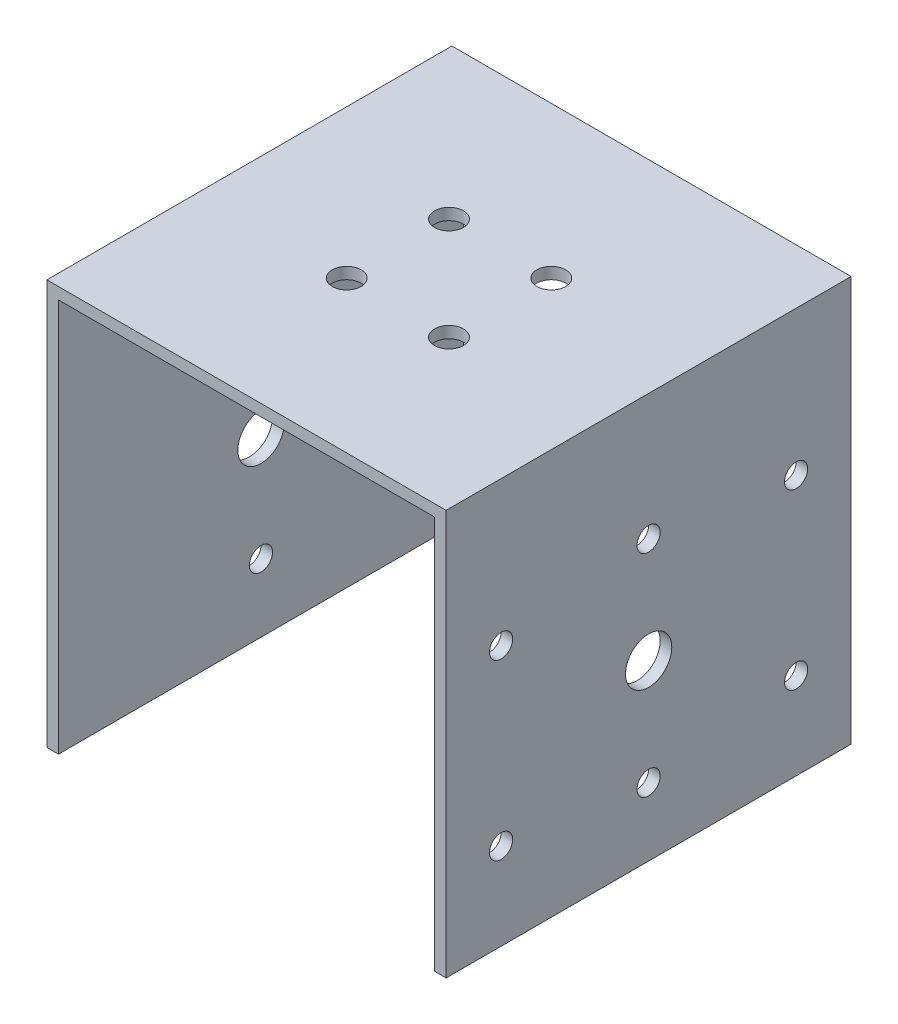
SolidWorks part; units mm, degrees
material "Liga 1060"
ref_plane "Plano frontal" through (0, 0, 0) normal (0, 0, 1) x (1, 0, 0)
ref_plane "Plano superior" through (0, 0, 0) normal (0, 1, 0) x (1, 0, 0)
ref_plane "Plano direito" through (0, 0, 0) normal (1, 0, 0) x (0, 0, -1)
sketch "Esboço1" plane through (0, 0, 0) normal (0, 0, 1) x (1, 0, 0)
  line L2 (32, -15) -> (32, 55)
  line L3 (32, 55) -> (-32, 55)
  line L4 (-32, -15) -> (-32, 55)
  line L5 (-30, -13) -> (-30, 53)
  line L6 (30, 53) -> (-30, 53)
  line L7 (30, -13) -> (30, 53)
  line L10 (-32, -15) -> (-30, -15)
  line L11 (-30, -15) -> (-30, -13)
  line L12 (30, -13) -> (30, -15)
  line L13 (30, -15) -> (32, -15)
  point P0 (0, 0)
  point P13 (0, 53)
  dimension "D1" = 64
  dimension "D2" = 70
  dimension "D4" = 60
  dimension "D3" = 2
extrude "Ressalto-extrusão1" add sketch "Esboço1" along normal blind 60
sketch "Esboço2" plane through (32, 0, 0) normal (1, 0, 0) x (0, 0, -1)
  line L0 (-60, 55) -> (0, 55) construction
  line L3 (0, -15) -> (0, 55) construction
  circle A0 centre (-30, 15) radius 4
  dimension "D2" = 8
  dimension "D1" = 40
  dimension "D3" = 30
extrude "Corte-extrusão1" cut sketch "Esboço2" against normal through all
sketch "Esboço3" plane through (0, 53, 0) normal (0, -1, 0) x (1, 0, 0)
  circle A0 centre (-8.8388, 38.8388) radius 2.5 construction
  circle A1 centre (-8.8388, 21.1612) radius 2.5 construction
  circle A2 centre (8.8388, 21.1612) radius 2.5 construction
  circle A3 centre (8.8388, 38.8388) radius 2.5 construction
  circle A4 centre (-8.8388, 38.8388) radius 2.5
  circle A5 centre (-8.8388, 21.1612) radius 2.5
  circle A6 centre (8.8388, 21.1612) radius 2.5
  circle A7 centre (8.8388, 38.8388) radius 2.5
extrude "Corte-extrusão2" cut sketch "Esboço3" against normal blind 10
sketch "Esboço4" plane through (0, 0, 60) normal (0, 0, 1) x (1, 0, 0)
  line L8 (-32, 55) -> (-32, -15)
  line L9 (-32, -15) -> (-30, -15)
  line L10 (-30, -15) -> (-30, 53)
  line L11 (-30, 53) -> (30, 53)
  line L12 (30, 53) -> (30, -15)
  line L13 (30, -15) -> (32, -15)
  line L14 (32, -15) -> (32, 55)
  line L15 (32, 55) -> (-32, 55)
  line L16 (-32, 55) -> (-32, -15)
  line L17 (-32, -15) -> (-30, -15)
  line L18 (-30, -15) -> (-30, 53)
  line L19 (-30, 53) -> (30, 53)
  line L20 (30, 53) -> (30, -15)
  line L21 (30, -15) -> (32, -15)
  line L22 (32, -15) -> (32, 55)
  line L23 (32, 55) -> (-32, 55)
  dimension "D1" = 0
extrude "Ressalto-extrusão2" add sketch "Esboço4" along normal blind 5
sketch "Esboço5" plane through (0, 0, 0) normal (0, 0, -1) x (-1, 0, 0)
  line L8 (32, -15) -> (32, 55)
  line L9 (32, 55) -> (-32, 55)
  line L10 (-32, 55) -> (-32, -15)
  line L11 (-32, -15) -> (-30, -15)
  line L12 (-30, -15) -> (-30, 53)
  line L13 (-30, 53) -> (30, 53)
  line L14 (30, 53) -> (30, -15)
  line L15 (30, -15) -> (32, -15)
  line L16 (32, -15) -> (32, 55)
  line L17 (32, 55) -> (-32, 55)
  line L18 (-32, 55) -> (-32, -15)
  line L19 (-32, -15) -> (-30, -15)
  line L20 (-30, -15) -> (-30, 53)
  line L21 (-30, 53) -> (30, 53)
  line L22 (30, 53) -> (30, -15)
  line L23 (30, -15) -> (32, -15)
  dimension "D1" = 0
extrude "Ressalto-extrusão3" add sketch "Esboço5" along normal blind 5
sketch "Esboço6" plane through (32, 0, 0) normal (1, 0, 0) x (0, 0, -1)
  circle A0 centre (-4.5, 0) radius 2 construction
  circle A1 centre (-4.5, 30) radius 2 construction
  circle A2 centre (-55.5, 0) radius 2 construction
  circle A3 centre (-55.5, 30) radius 2 construction
  circle A4 centre (-4.5, 0) radius 2
  circle A5 centre (-4.5, 30) radius 2
  circle A6 centre (-55.5, 0) radius 2
  circle A7 centre (-55.5, 30) radius 2
extrude "Corte-extrusão3" cut sketch "Esboço6" against normal blind 10
sketch "Esboço7" plane through (32, 0, 0) normal (1, 0, 0) x (0, 0, -1)
  line L4 (-65, -15) -> (5, -15)
  line L5 (5, -15) -> (5, 55)
  line L6 (5, 55) -> (-65, 55)
  line L7 (-65, 55) -> (-65, -15)
  line L8 (-65, -15) -> (5, -15)
  line L9 (5, -15) -> (5, 55)
  line L10 (5, 55) -> (-65, 55)
  line L11 (-65, 55) -> (-65, -15)
  circle A0 centre (-55.5, 0) radius 2 construction
  circle A1 centre (-55.5, 30) radius 2 construction
  circle A2 centre (-30, 15) radius 4 construction
  circle A3 centre (-4.5, 0) radius 2 construction
  circle A4 centre (-4.5, 30) radius 2 construction
  circle A5 centre (-55.5, 0) radius 2
  circle A6 centre (-55.5, 30) radius 2
  circle A7 centre (-30, 15) radius 4
  circle A8 centre (-4.5, 0) radius 2
  circle A9 centre (-4.5, 30) radius 2
  dimension "D1" = 0
extrude "Ressalto-extrusão4" add sketch "Esboço7" along normal blind 2.5
sketch "Esboço8" plane through (-32, 0, 0) normal (-1, 0, 0) x (0, 0, 1)
  line L4 (65, 55) -> (-5, 55)
  line L5 (-5, 55) -> (-5, -15)
  line L6 (-5, -15) -> (65, -15)
  line L7 (65, -15) -> (65, 55)
  line L8 (65, 55) -> (-5, 55)
  line L9 (-5, 55) -> (-5, -15)
  line L10 (-5, -15) -> (65, -15)
  line L11 (65, -15) -> (65, 55)
  circle A0 centre (30, 15) radius 4 construction
  circle A1 centre (30, 15) radius 4
  dimension "D1" = 0
extrude "Ressalto-extrusão5" add sketch "Esboço8" along normal blind 2.5
sketch "Esboço9" plane through (30, 0, 0) normal (-1, 0, 0) x (0, 0, 1)
  line L4 (65, 53) -> (-5, 53)
  line L5 (-5, 53) -> (-5, -15)
  line L6 (-5, -15) -> (65, -15)
  line L7 (65, -15) -> (65, 53)
  line L8 (65, 53) -> (-5, 53)
  line L9 (-5, 53) -> (-5, -15)
  line L10 (-5, -15) -> (65, -15)
  line L11 (65, -15) -> (65, 53)
  dimension "D1" = 0
extrude "Corte-extrusão4" cut sketch "Esboço9" against normal blind 2.5
sketch "Esboço10" plane through (-30, 0, 0) normal (1, 0, 0) x (0, 0, -1)
  line L4 (-65, -15) -> (5, -15)
  line L5 (5, -15) -> (5, 53)
  line L6 (5, 53) -> (-65, 53)
  line L7 (-65, 53) -> (-65, -15)
  line L8 (-65, -15) -> (5, -15)
  line L9 (5, -15) -> (5, 53)
  line L10 (5, 53) -> (-65, 53)
  line L11 (-65, 53) -> (-65, -15)
  dimension "D1" = 0
extrude "Corte-extrusão5" cut sketch "Esboço10" against normal blind 2.5
sketch "Esboço11" plane through (34.5, 0, 0) normal (1, 0, 0) x (0, 0, -1)
  circle A0 centre (-30, -3.25) radius 2
  circle A1 centre (-30, 33.25) radius 2
  circle A2 centre (-30, 15) radius 4 construction
  point P6 (0, 0)
  point P7 (0, 0)
  point P8 (-27.1176, 17.7734)
  dimension "D1" = 4
  dimension "D2" = 4
  dimension "D3" = 36.5
  dimension "D4" = 18.25
  dimension "D5" = 18.25
extrude "Corte-extrusão6" cut sketch "Esboço11" against normal through all
